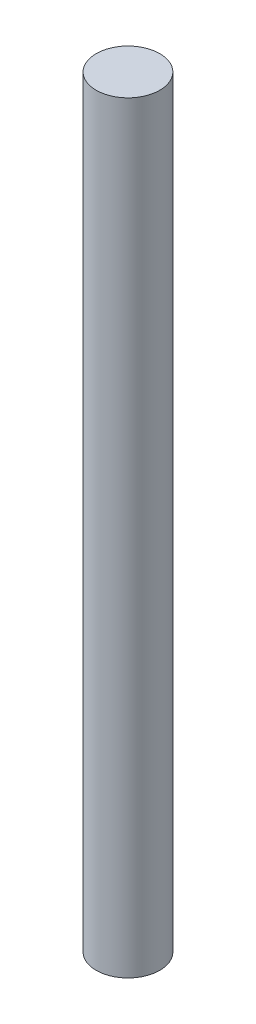
SolidWorks part; units mm, degrees
material "1060 Alloy"
ref_plane "Front Plane" through (0, 0, 0) normal (0, 0, 1) x (1, 0, 0)
ref_plane "Top Plane" through (0, 0, 0) normal (0, 1, 0) x (1, 0, 0)
ref_plane "Right Plane" through (0, 0, 0) normal (1, 0, 0) x (0, 0, -1)
sketch "Sketch1" plane through (0, 0, 0) normal (0, 1, 0) x (1, 0, 0)
  circle A0 centre (0, 0) radius 1.875
  dimension "D1" = 3.75
extrude "Boss-Extrude1" add sketch "Sketch1" along normal blind 45
